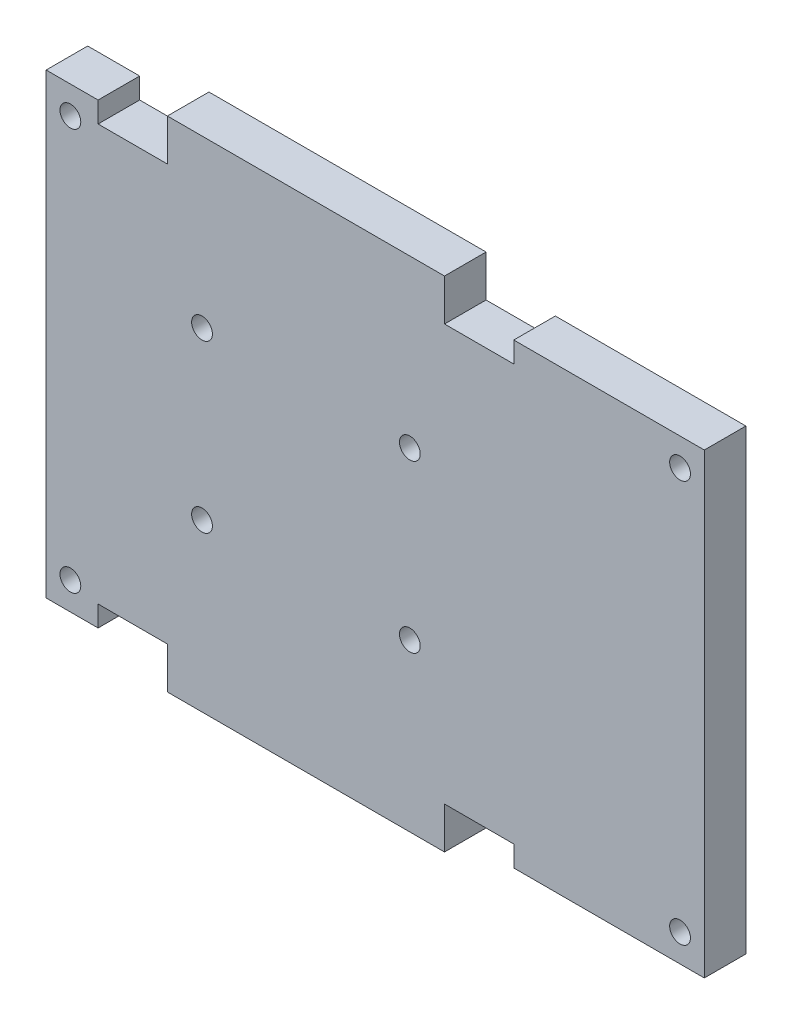
SolidWorks part; units mm, degrees
material "Acrylic (Medium-high impact)"
ref_plane "Front Plane" through (0, 0, 0) normal (0, 0, 1) x (1, 0, 0)
ref_plane "Top Plane" through (0, 0, 0) normal (0, 1, 0) x (1, 0, 0)
ref_plane "Right Plane" through (0, 0, 0) normal (1, 0, 0) x (0, 0, -1)
sketch "Sketch1" plane through (0, 0, 0) normal (0, 0, 1) x (1, 0, 0)
  line L1 (-30, -36) -> (30, -36)
  line L2 (-30, -36) -> (-30, 36)
  line L3 (-30, 36) -> (30, 36)
  line L4 (30, -36) -> (30, 36)
  line L5 (-30, -36) -> (30, 36) construction
  line L6 (-30, 36) -> (30, -36) construction
  point P0 (0, 0)
  dimension "D1" = 72
  dimension "D2" = 60
extrude "Boss-Extrude1" add sketch "Sketch1" along normal blind 6
sketch "Sketch2" plane through (0, 0, 6) normal (0, 0, 1) x (1, 0, 0)
  line L0 (0, 0) -> (-30, 0) construction
  line L1 (-30, 36) -> (-20, 36)
  line L2 (-30, 36) -> (-30, 30)
  line L3 (-30, 30) -> (-20, 30)
  line L4 (-20, 36) -> (-20, 30)
  line L5 (-30, 36) -> (-30, -36) construction
  line L6 (-30, 0) -> (0, 0) construction
  line L7 (0, 0) -> (0, 36) construction
  line L8 (30, 36) -> (-30, 36) construction
  line L9 (-30, -30) -> (-20, -30)
  line L10 (-20, -36) -> (-20, -30)
  line L11 (-30, -36) -> (-20, -36)
  line L12 (-30, -36) -> (-30, -30)
  line L13 (30, -36) -> (30, -30)
  line L14 (30, -36) -> (20, -36)
  line L15 (20, -36) -> (20, -30)
  line L16 (30, -30) -> (20, -30)
  line L17 (30, 30) -> (20, 30)
  line L18 (20, 36) -> (20, 30)
  line L19 (30, 36) -> (20, 36)
  line L20 (30, 36) -> (30, 30)
  dimension "D1" = 6
  dimension "D2" = 10
extrude "Cut-Extrude1" cut sketch "Sketch2" against normal through all both and the other way through all
sketch "Sketch3" plane through (0, 0, 6) normal (0, 0, 1) x (1, 0, 0)
  line L1 (-15, -12) -> (15, -12) construction
  line L2 (-15, -12) -> (-15, 12) construction
  line L3 (-15, 12) -> (15, 12) construction
  line L4 (15, -12) -> (15, 12) construction
  line L5 (-15, -12) -> (15, 12) construction
  line L6 (-15, 12) -> (15, -12) construction
  circle A0 centre (-15, 12) radius 1.5
  circle A1 centre (-15, -12) radius 1.5
  circle A2 centre (15, -12) radius 1.5
  circle A3 centre (15, 12) radius 1.5
  point P0 (0, 0)
  dimension "D3" = 3
  dimension "D1" = 30
  dimension "D2" = 24
extrude "Cut-Extrude2" cut sketch "Sketch3" against normal through all both
sketch "Sketch6" plane through (30, 0, 0) normal (1, 0, 0) x (0, 0, -1)
  line L0 (-6, 30) -> (-6, 36) construction
  line L1 (-6, 33) -> (0, 33)
  line L2 (-6, 33) -> (-6, -33)
  line L3 (-6, -33) -> (0, -33)
  line L4 (0, 33) -> (0, -33)
  line L5 (0, -30) -> (0, -36) construction
  dimension "D1" = 66
extrude "Boss-Extrude2" add sketch "Sketch6" along normal blind 27.5
sketch "Sketch7" plane through (-30, 0, 0) normal (-1, 0, 0) x (0, 0, 1)
  line L0 (0, 30) -> (0, 36) construction
  line L1 (0, 33) -> (6, 33)
  line L2 (0, 33) -> (0, -33)
  line L3 (0, -33) -> (6, -33)
  line L4 (6, 33) -> (6, -33)
  line L5 (6, -30) -> (6, -36) construction
  point P8 (0, 0)
  dimension "D1" = 66
extrude "Boss-Extrude3" add sketch "Sketch7" along normal blind 7.5
sketch "Sketch8" plane through (0, 0, 6) normal (0, 0, 1) x (1, 0, 0)
  line L0 (57.5, -33) -> (30, -33) construction
  line L1 (57.5, 33) -> (57.5, -33) construction
  line L2 (57.5, 33) -> (30, 33) construction
  line L3 (-37.5, -33) -> (-37.5, 33) construction
  circle A0 centre (54, -29) radius 1.5
  circle A1 centre (54, 29) radius 1.5
  circle A2 centre (-34, 29) radius 1.5
  circle A3 centre (-34, -29) radius 1.5
  dimension "D1" = 4
  dimension "D3" = 3
  dimension "D5" = 3.5
  dimension "D2" = 3.5
  dimension "D4" = 4
extrude "Cut-Extrude3" cut sketch "Sketch8" against normal through all
